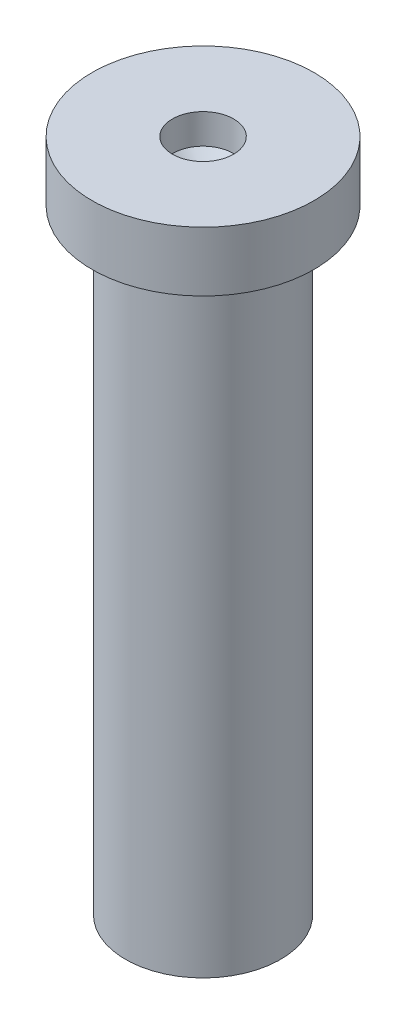
SolidWorks part; units mm, degrees
ref_plane "Front Plane" through (0, 0, 0) normal (0, 0, 1) x (1, 0, 0)
ref_plane "Top Plane" through (0, 0, 0) normal (0, 1, 0) x (1, 0, 0)
ref_plane "Right Plane" through (0, 0, 0) normal (1, 0, 0) x (0, 0, -1)
sketch "Sketch1" plane through (0, 0, 0) normal (0, 0, 1) x (1, 0, 0)
  line L0 (-0.9307, -5.3286) -> (0.3693, -5.3286)
  line L1 (0.3693, -5.3286) -> (0.3693, 4.9714)
  line L2 (0.3693, 4.9714) -> (0.9307, 4.9714)
  line L3 (0.9307, 4.9714) -> (0.9307, 5.9714)
  line L4 (0.9307, 5.9714) -> (-0.4176, 5.9714)
  line L6 (-0.9307, -5.3286) -> (-0.9307, 5.0194)
  line L7 (-0.4176, 5.9714) -> (-0.4176, 5.4688)
  line L8 (-0.4176, 5.4688) -> (-0.9307, 5.0194)
  dimension "D1" = 10.3
  dimension "D2" = 1
revolve "Revolve1" add sketch "Sketch1" angle 360 about L6
